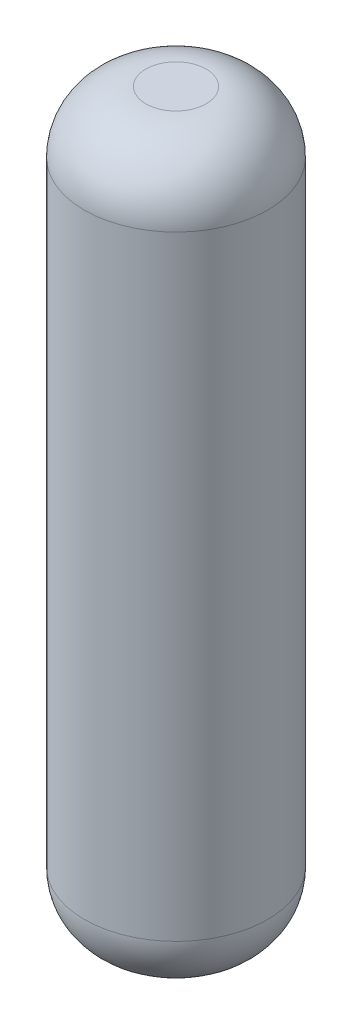
SolidWorks part; units mm, degrees
ref_plane "Front Plane" through (0, 0, 0) normal (0, 0, 1) x (1, 0, 0)
ref_plane "Top Plane" through (0, 0, 0) normal (0, 1, 0) x (1, 0, 0)
ref_plane "Right Plane" through (0, 0, 0) normal (1, 0, 0) x (0, 0, -1)
sketch "Sketch1" plane through (0, 0, 0) normal (0, 1, 0) x (1, 0, 0)
  circle A0 centre (0, 0) radius 75.7272
extrude "Boss-Extrude1" add sketch "Sketch1" along normal blind 609.6
fillet "Fillet1" radius 50.8 2 edges at (0, 0, 75.7272) (0, 609.6, 75.7272)
